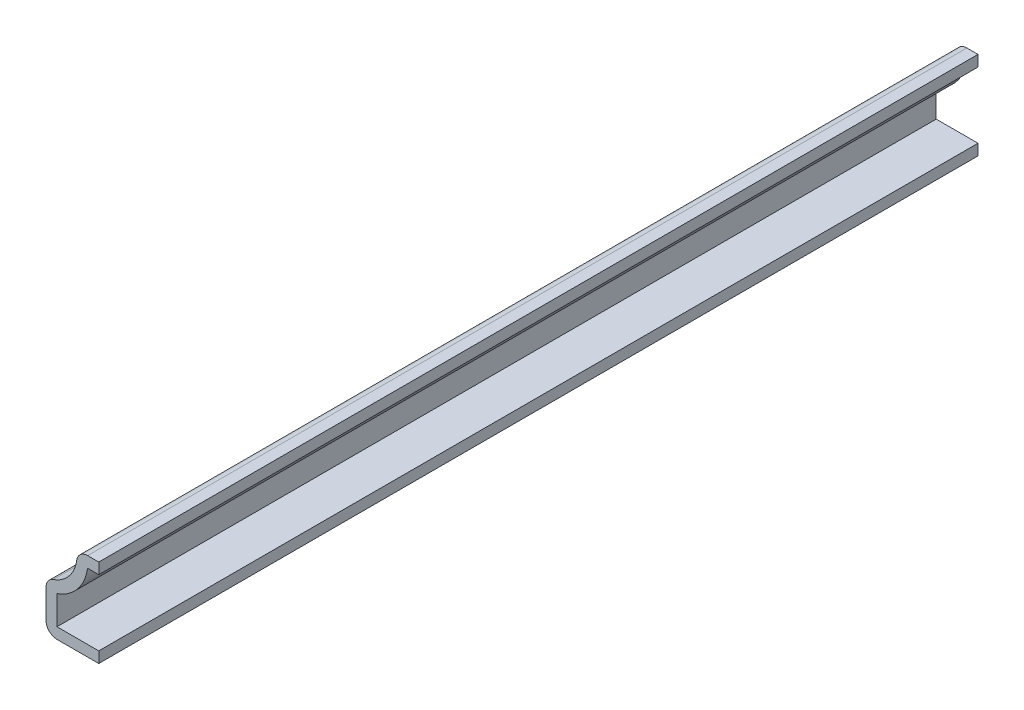
SolidWorks part; units mm, degrees
ref_plane "Front Plane" through (0, 0, 0) normal (0, 0, 1) x (1, 0, 0)
ref_plane "Top Plane" through (0, 0, 0) normal (0, 1, 0) x (1, 0, 0)
ref_plane "Right Plane" through (0, 0, 0) normal (1, 0, 0) x (0, 0, -1)
sketch "Sketch1" plane through (0, 0, 0) normal (0, 0, 1) x (1, 0, 0)
  line L0 (0, 0) -> (-9.525, 0)
  line L1 (-9.525, 0) -> (-9.525, 8.7312)
  line L2 (-3.9688, 15.875) -> (0, 15.875)
  line L3 (0, 15.875) -> (0, 0) construction
  arc A0 (-9.525, 8.7312) -> (-3.9688, 15.875) centre (-10.2634, 15.0382) ccw
  dimension "D4" = 6.35
  dimension "D1" = 15.875
  dimension "D2" = 9.525
  dimension "D3" = 8.7312
  dimension "D5" = 3.9688
extrude "Extrude-Thin1" add sketch "Sketch1" against normal blind 158.75 thin
fillet "Fillet1" radius 1.9812 3 edges at (-9.525, 0, -79.375) (-9.525, 8.7312, -79.375) (-3.9688, 15.875, -79.375)
